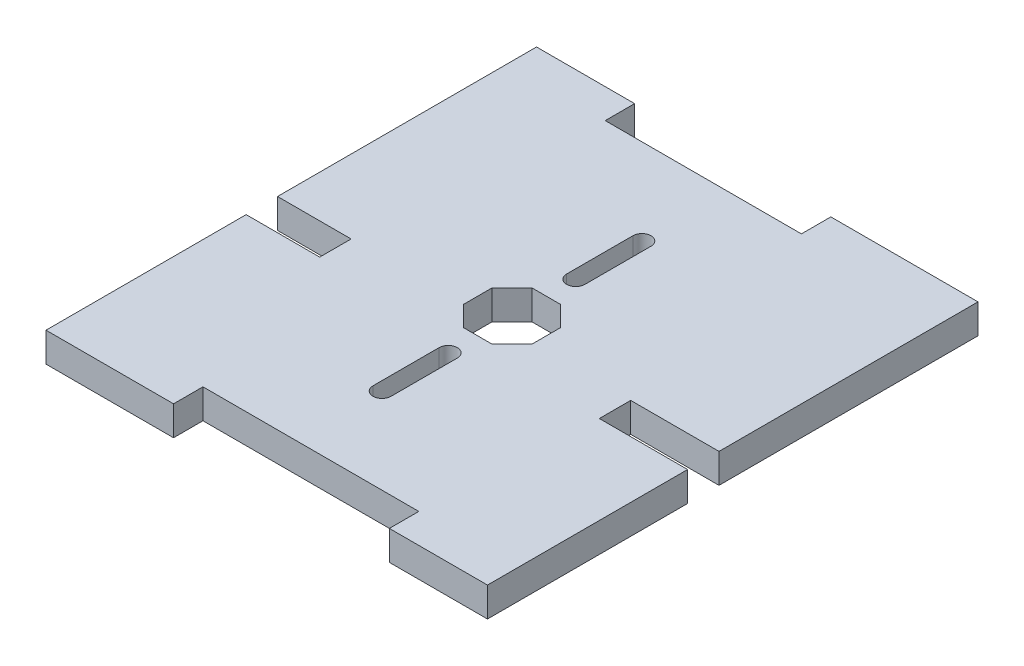
SolidWorks part; units mm, degrees
ref_plane "Front Plane" through (0, 0, 0) normal (0, 0, 1) x (1, 0, 0)
ref_plane "Top Plane" through (0, 0, 0) normal (0, 1, 0) x (1, 0, 0)
ref_plane "Right Plane" through (0, 0, 0) normal (1, 0, 0) x (0, 0, -1)
sketch "Sketch1" plane through (0, 0, 0) normal (0, 1, 0) x (1, 0, 0)
  line L1 (0, 0) -> (45, 0)
  line L2 (0, 0) -> (0, 50)
  line L3 (0, 50) -> (45, 50)
  line L4 (45, 0) -> (45, 50)
  dimension "D1" = 50
  dimension "D2" = 45
extrude "Boss-Extrude1" add sketch "Sketch1" along normal blind 3
sketch "Sketch2" plane through (0, 3, 0) normal (0, 1, 0) x (1, 0, 0)
  line L0 (45, 50) -> (0, 50) construction
  line L1 (10, 50) -> (30, 50)
  line L2 (10, 50) -> (10, 47)
  line L3 (10, 47) -> (30, 47)
  line L4 (30, 50) -> (30, 47)
  line L5 (0, 50) -> (0, 0) construction
  line L6 (0, 0) -> (45, 0) construction
  line L7 (13, 0) -> (35, 0)
  line L8 (13, 0) -> (13, 3)
  line L9 (13, 3) -> (35, 3)
  line L10 (35, 0) -> (35, 3)
  line L11 (45, 0) -> (45, 50) construction
  line L12 (0, 23.5) -> (7.5, 23.5)
  line L13 (0, 23.5) -> (0, 20.5)
  line L14 (0, 20.5) -> (7.5, 20.5)
  line L15 (7.5, 23.5) -> (7.5, 20.5)
  line L16 (45, 23.5) -> (36, 23.5)
  line L17 (45, 23.5) -> (45, 20.5)
  line L18 (45, 20.5) -> (36, 20.5)
  line L19 (36, 23.5) -> (36, 20.5)
  line L20 (22.5, 31.5) -> (22.5, 38.25) construction
  line L21 (21.0503, 21.5) -> (23.9497, 21.5)
  line L22 (23.9497, 21.5) -> (26, 23.5503)
  line L23 (26, 23.5503) -> (26, 26.4497)
  line L24 (26, 26.4497) -> (23.9497, 28.5)
  line L25 (23.9497, 28.5) -> (21.0503, 28.5)
  line L26 (21.0503, 28.5) -> (19, 26.4497)
  line L27 (19, 26.4497) -> (19, 23.5503)
  line L28 (19, 23.5503) -> (21.0503, 21.5)
  line L29 (21.575, 31.5) -> (21.575, 38.25)
  line L30 (23.425, 31.5) -> (23.425, 38.25)
  line L31 (22.5, 18.5) -> (22.5, 11.75) construction
  line L32 (23.425, 18.5) -> (23.425, 11.75)
  line L33 (21.575, 18.5) -> (21.575, 11.75)
  circle A0 centre (22.5, 25) radius 3.7884 construction
  arc A1 (21.575, 31.5) -> (23.425, 31.5) centre (22.5, 31.5) ccw
  arc A2 (23.425, 38.25) -> (21.575, 38.25) centre (22.5, 38.25) ccw
  arc A3 (23.425, 18.5) -> (21.575, 18.5) centre (22.5, 18.5) ccw
  arc A4 (21.575, 11.75) -> (23.425, 11.75) centre (22.5, 11.75) ccw
  point P25 (22.5, 34.875)
  point P41 (22.5, 15.125)
  dimension "D17" = 3
  dimension "D18" = 6.75
  dimension "D1" = 20
  dimension "D2" = 10
  dimension "D3" = 3
  dimension "D4" = 22
  dimension "D5" = 3
  dimension "D6" = 13
  dimension "D7" = 7.5
  dimension "D8" = 9
  dimension "D9" = 3
  dimension "D10" = 20.5
  dimension "D11" = 18.5
  dimension "D12" = 18.5
  dimension "D13" = 19
  dimension "D14" = 19
  dimension "D15" = 1.85
  dimension "D16" = 3
extrude "Cut-Extrude1" cut sketch "Sketch2" against normal through all
sketch "Sketch3" plane through (0, 0, 0) normal (0, 0, 1) x (1, 0, 0)
  line L0 (45, 3) -> (45, 0) construction
  line L1 (0, 3) -> (45, 3)
  line L2 (0, 3) -> (0, 2.9)
  line L3 (0, 2.9) -> (45, 2.9)
  line L4 (45, 3) -> (45, 2.9)
  line L6 (0, 0) -> (45, 0)
  line L7 (0, 0) -> (0, 0.1)
  line L8 (0, 0.1) -> (45, 0.1)
  line L9 (45, 0) -> (45, 0.1)
  dimension "D1" = 0.1
ref_plane "Plane5" through (0, 0, -25) normal (0, 0, 1) x (1, 0, 0)
sketch "Sketch4" plane through (0, 3, 0) normal (0, 1, 0) x (1, 0, 0)
  line L0 (36, 23.5) -> (36, 20.5) construction
  line L1 (0, 23.5) -> (7.5, 23.5)
  line L2 (0, 23.5) -> (0, 23.6)
  line L3 (0, 23.6) -> (7.5, 23.6)
  line L4 (7.5, 23.5) -> (7.5, 23.6)
  line L5 (0, 20.5) -> (7.5, 20.5)
  line L6 (0, 20.5) -> (0, 20.4)
  line L7 (0, 20.4) -> (7.5, 20.4)
  line L8 (7.5, 20.5) -> (7.5, 20.4)
  line L9 (45, 20.5) -> (36, 20.5)
  line L10 (45, 20.5) -> (45, 20.4)
  line L11 (45, 20.4) -> (36, 20.4)
  line L12 (36, 20.5) -> (36, 20.4)
  line L13 (45, 23.5) -> (36, 23.5)
  line L14 (45, 23.5) -> (45, 23.6)
  line L15 (45, 23.6) -> (36, 23.6)
  line L16 (36, 23.5) -> (36, 23.6)
  line L17 (7.5, 20.5) -> (7.5, 23.5) construction
  dimension "D1" = 0.1
extrude "Cut-Extrude2" cut sketch "Sketch4" against normal through all
